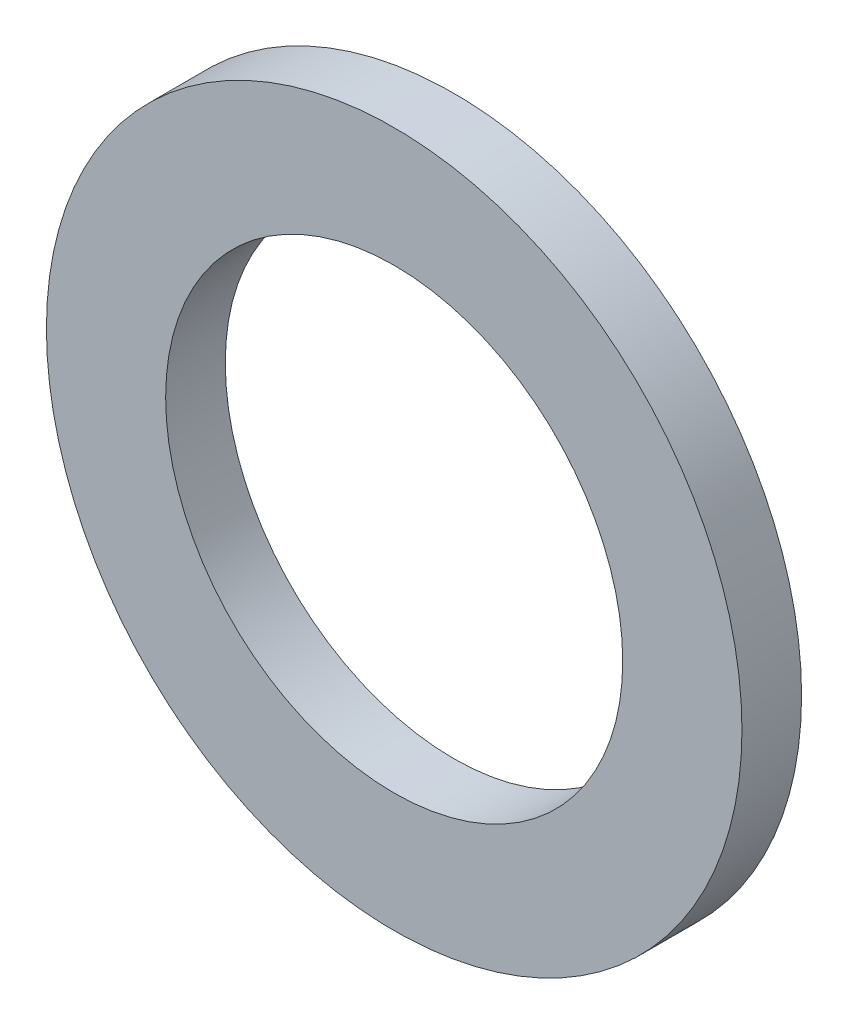
SolidWorks part; units mm, degrees
ref_plane "Front Plane" through (0, 0, 0) normal (0, 0, 1) x (1, 0, 0)
ref_plane "Top Plane" through (0, 0, 0) normal (0, 1, 0) x (1, 0, 0)
ref_plane "Right Plane" through (0, 0, 0) normal (1, 0, 0) x (0, 0, -1)
sketch "Sketch1" plane through (0, 0, 0) normal (0, 0, 1) x (1, 0, 0)
  circle A0 centre (0, 0) radius 11.5
  circle A1 centre (0, 0) radius 17.5
  dimension "D1" = 23
  dimension "D2" = 35
extrude "Boss-Extrude1" add sketch "Sketch1" along normal blind 3
